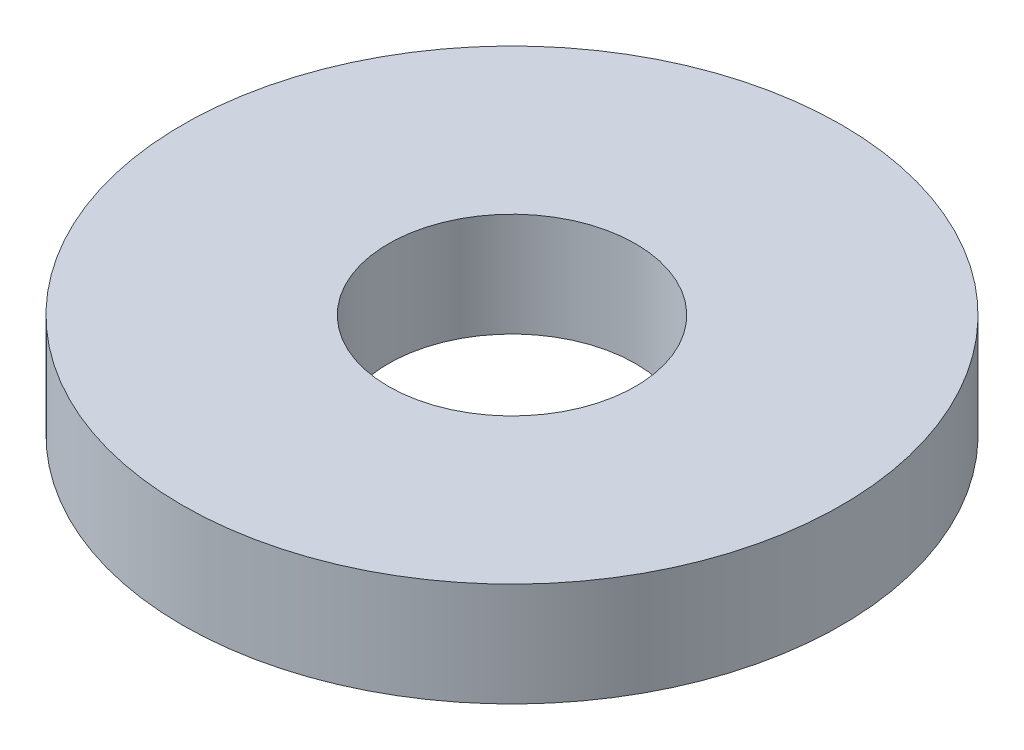
SolidWorks part; units mm, degrees
ref_plane "Front Plane" through (0, 0, 0) normal (0, 0, 1) x (1, 0, 0)
ref_plane "Top Plane" through (0, 0, 0) normal (0, 1, 0) x (1, 0, 0)
ref_plane "Right Plane" through (0, 0, 0) normal (1, 0, 0) x (0, 0, -1)
sketch "Sketch1" plane through (0, 0, 0) normal (0, 1, 0) x (1, 0, 0)
  circle A0 centre (0, 0) radius 4.7625
  circle A1 centre (0, 0) radius 12.7
  dimension "D1" = 9.525
  dimension "D2" = 25.4
extrude "Boss-Extrude1" add sketch "Sketch1" along normal blind 4
